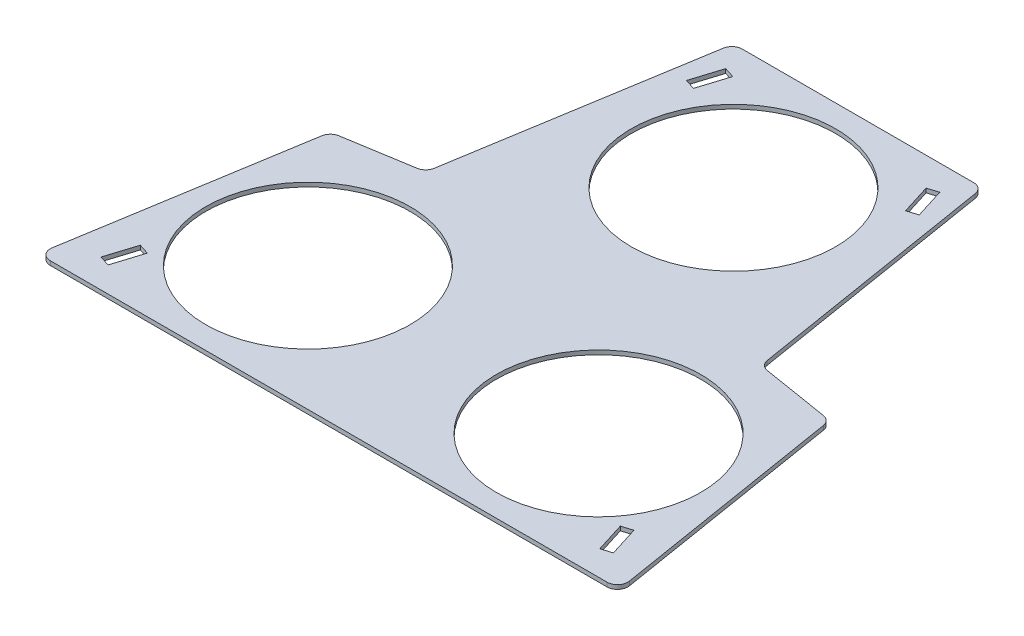
SolidWorks part; units mm, degrees
material "Acrylic (Medium-high impact)"
ref_plane "Front Plane" through (0, 0, 0) normal (0, 0, 1) x (1, 0, 0)
ref_plane "Top Plane" through (0, 0, 0) normal (0, 1, 0) x (1, 0, 0)
ref_plane "Right Plane" through (0, 0, 0) normal (1, 0, 0) x (0, 0, -1)
sketch "Sketch1" plane through (0, 0, 0) normal (0, 1, 0) x (1, 0, 0)
  line L0 (-134.1189, 0) -> (134.1189, 0)
  line L1 (139.0537, 5.8045) -> (120.843, 117.5127)
  line L2 (116.7126, 121.6431) -> (84.3366, 126.921)
  line L3 (80.2062, 131.0514) -> (60.684, 250.8045)
  line L4 (-55.7491, 255) -> (55.7491, 255)
  line L6 (-60.684, 250.8045) -> (-80.2062, 131.0514)
  line L7 (-84.3366, 126.921) -> (-116.7126, 121.6431)
  line L8 (-120.843, 117.5127) -> (-139.0537, 5.8045)
  line L9 (0, 0) -> (0, 255) construction
  circle A0 centre (0, 195) radius 49.25
  circle A1 centre (-70, 60) radius 49.25
  circle A2 centre (70, 60) radius 49.25
  arc A3 (-116.7126, 121.6431) -> (-120.843, 117.5127) centre (-115.9081, 116.7082) ccw
  arc A4 (-80.2062, 131.0514) -> (-84.3366, 126.921) centre (-85.1411, 131.8559) cw
  arc A5 (84.3366, 126.921) -> (80.2062, 131.0514) centre (85.1411, 131.8559) cw
  arc A6 (120.843, 117.5127) -> (116.7126, 121.6431) centre (115.9081, 116.7082) ccw
  arc A7 (134.1189, 0) -> (139.0537, 5.8045) centre (134.1189, 5) ccw
  arc A8 (60.684, 250.8045) -> (55.7491, 255) centre (55.7491, 250) ccw
  arc A9 (-55.7491, 255) -> (-60.684, 250.8045) centre (-55.7491, 250) ccw
  arc A10 (-139.0537, 5.8045) -> (-134.1189, 0) centre (-134.1189, 5) ccw
  point P19 (-120.264, 121.0641)
  point P22 (-80.7852, 127.5)
  point P25 (80.7852, 127.5)
  point P28 (120.264, 121.0641)
  point P31 (140, 0)
  point P34 (60, 255)
  point P37 (-60, 255)
  point P40 (-140, 0)
  dimension "D1" = 98.5
  dimension "D12" = 5
  dimension "D4" = 60
  dimension "D5" = 60
  dimension "D6" = 140
  dimension "D7" = 135
  dimension "D8" = 127.5
  dimension "D9" = 280
  dimension "D10" = 120
  dimension "D11" = 40
extrude "Boss-Extrude1" add sketch "Sketch1" along normal blind 2
sketch "Sketch2" plane through (0, 2, 0) normal (0, 1, 0) x (1, 0, 0)
  line L0 (0, 0) -> (0, 255) construction
  line L1 (55.7491, 255) -> (-55.7491, 255) construction
  line L2 (-125, 0) -> (-45, 255) construction
  line L3 (-56.0889, 228.4234) -> (-51.5689, 242.8311)
  line L4 (-134.1189, 0) -> (134.1189, 0) construction
  line L5 (-56.0889, 228.4234) -> (-51.0796, 226.8519)
  line L6 (-51.5689, 242.8311) -> (-46.5596, 241.2595)
  line L7 (-51.0796, 226.8519) -> (-46.5596, 241.2595)
  line L8 (-56.0889, 228.4234) -> (-46.5596, 241.2595) construction
  line L9 (-51.5689, 242.8311) -> (-51.0796, 226.8519) construction
  line L10 (113.9111, 26.5766) -> (123.4404, 13.7405) construction
  line L11 (-118.4311, 12.1689) -> (-113.9111, 26.5766)
  line L12 (-118.4311, 12.1689) -> (-123.4404, 13.7405)
  line L13 (-113.9111, 26.5766) -> (-118.9204, 28.1481)
  line L14 (-123.4404, 13.7405) -> (-118.9204, 28.1481)
  line L15 (-118.4311, 12.1689) -> (-118.9204, 28.1481) construction
  line L16 (-113.9111, 26.5766) -> (-123.4404, 13.7405) construction
  line L17 (118.4311, 12.1689) -> (118.9204, 28.1481) construction
  line L18 (51.5689, 242.8311) -> (51.0796, 226.8519) construction
  line L19 (56.0889, 228.4234) -> (46.5596, 241.2595) construction
  line L20 (125, 0) -> (45, 255) construction
  line L21 (123.4404, 13.7405) -> (118.9204, 28.1481)
  line L22 (113.9111, 26.5766) -> (118.9204, 28.1481)
  line L23 (118.4311, 12.1689) -> (123.4404, 13.7405)
  line L24 (118.4311, 12.1689) -> (113.9111, 26.5766)
  line L25 (51.0796, 226.8519) -> (46.5596, 241.2595)
  line L26 (51.5689, 242.8311) -> (46.5596, 241.2595)
  line L27 (56.0889, 228.4234) -> (51.0796, 226.8519)
  line L28 (56.0889, 228.4234) -> (51.5689, 242.8311)
  line L29 (-85, 127.5) -> (-208.5894, 166.2732) construction
  point P10 (-51.3242, 234.8415)
  point P13 (-118.6758, 20.1585)
  point P31 (118.6758, 20.1585)
  point P32 (51.3242, 234.8415)
  dimension "D1" = 45
  dimension "D3" = 5.25
  dimension "D4" = 15.1
  dimension "D5" = 209.9
  dimension "D6" = 125
extrude "Cut-Extrude1" cut sketch "Sketch2" against normal blind 5
